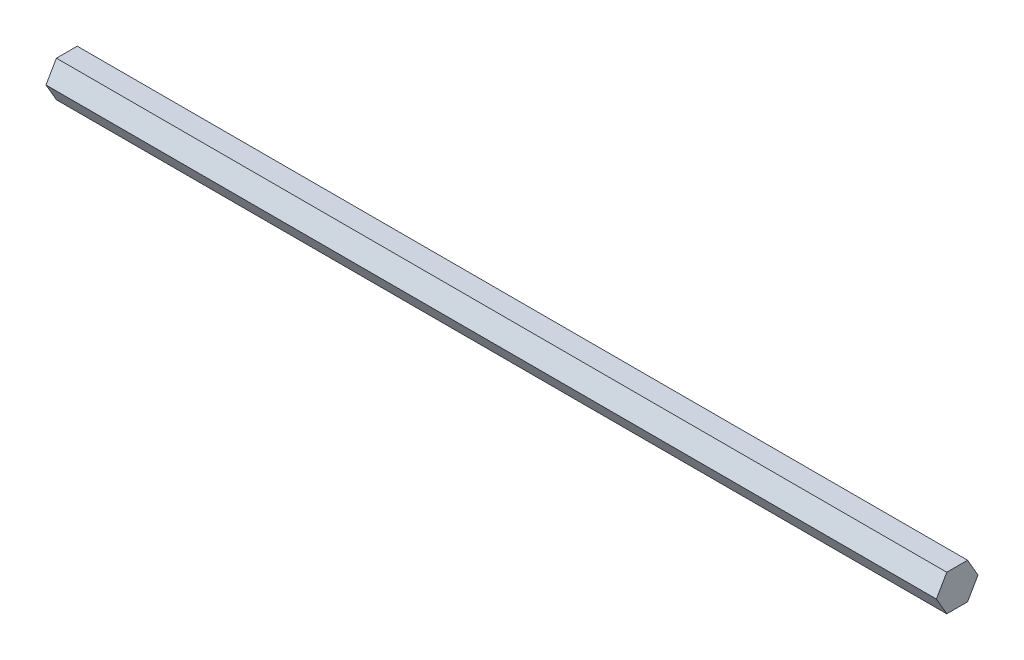
SolidWorks part; units mm, degrees
ref_plane "Front Plane" through (0, 0, 0) normal (0, 0, 1) x (1, 0, 0)
ref_plane "Top Plane" through (0, 0, 0) normal (0, 1, 0) x (1, 0, 0)
ref_plane "Right Plane" through (0, 0, 0) normal (1, 0, 0) x (0, 0, -1)
sketch "Sketch1" plane through (0, 0, 0) normal (1, 0, 0) x (0, 0, -1)
  line L1 (7.3323, 0) -> (3.6662, 6.35)
  line L2 (3.6662, 6.35) -> (-3.6662, 6.35)
  line L3 (-3.6662, 6.35) -> (-7.3323, 0)
  line L4 (-7.3323, 0) -> (-3.6662, -6.35)
  line L5 (-3.6662, -6.35) -> (3.6662, -6.35)
  line L6 (3.6662, -6.35) -> (7.3323, 0)
  circle A0 centre (0, 0) radius 6.35 construction
  dimension "D1" = 12.7
extrude "Boss-Extrude1" add sketch "Sketch1" along normal blind 313.7
